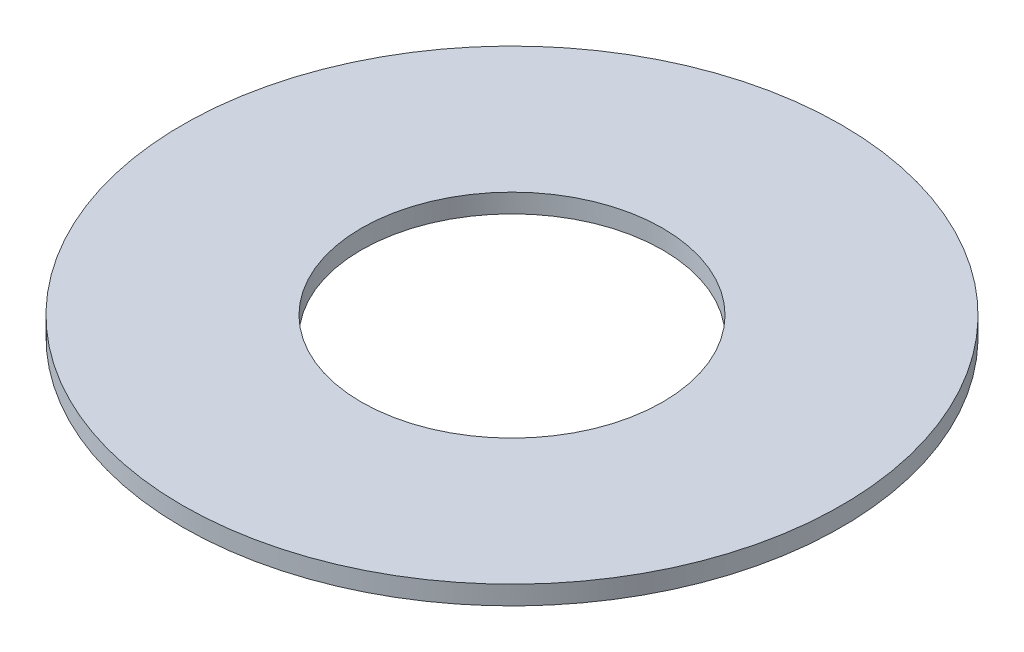
SolidWorks part; units mm, degrees
ref_plane "Alzado" through (0, 0, 0) normal (0, 0, 1) x (1, 0, 0)
ref_plane "Planta" through (0, 0, 0) normal (0, 1, 0) x (1, 0, 0)
ref_plane "Vista lateral" through (0, 0, 0) normal (1, 0, 0) x (0, 0, -1)
sketch "Sketch3" plane through (0, 0, 0) normal (0, 1, 0) x (1, 0, 0)
  circle A0 centre (0, 0) radius 1.6
  circle A1 centre (0, 0) radius 3.5
extrude "Boss-Extrude1" add sketch "Sketch3" along normal blind 0.2
